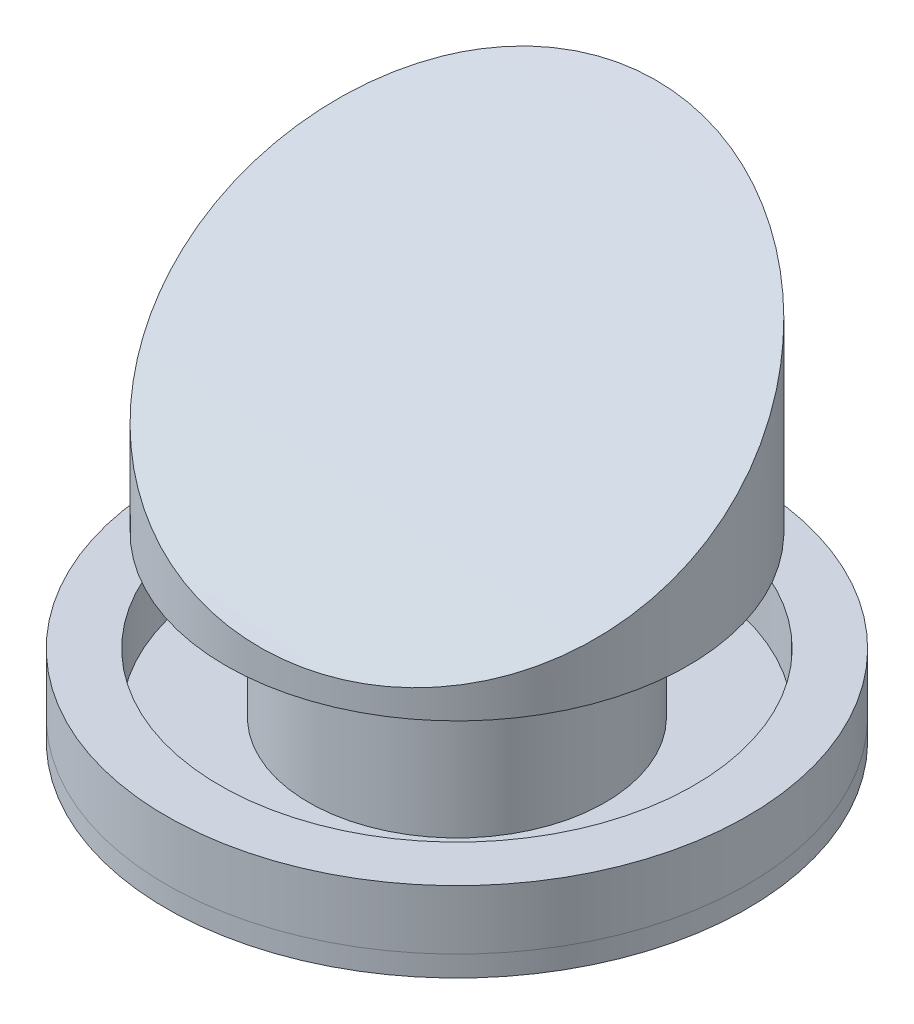
SolidWorks part; units mm, degrees
ref_plane "Plano frontal" through (0, 0, 0) normal (0, 0, 1) x (1, 0, 0)
ref_plane "Plano superior" through (0, 0, 0) normal (0, 1, 0) x (1, 0, 0)
ref_plane "Plano direito" through (0, 0, 0) normal (1, 0, 0) x (0, 0, -1)
sketch "Esboço2" plane through (0, 0, 0) normal (0, 0, 1) x (1, 0, 0)
  line L0 (0, 0) -> (0, 847.2146) construction
  line L1 (0, 0) -> (846.5488, 0) construction
  line L2 (0, 0) -> (490, 0)
  line L3 (490, 0) -> (490, 35)
  line L4 (490, 35) -> (250, 35)
  line L5 (250, 35) -> (250, 305)
  line L6 (250, 305) -> (390, 305)
  line L7 (390, 305) -> (390, 775)
  line L8 (390, 775) -> (0, 775)
  line L9 (0, 775) -> (0, 305)
  line L10 (0, 305) -> (230, 305)
  line L11 (230, 305) -> (230, 35)
  line L12 (230, 35) -> (0, 35)
  line L13 (0, 35) -> (0, 0)
  dimension "D1" = 35
  dimension "D2" = 980
  dimension "D3" = 270
  dimension "D4" = 20
  dimension "D5" = 500
  dimension "D6" = 470
  dimension "D7" = 780
revolve "Revolução1" add sketch "Esboço2" angle 360 about L0
sketch "Esboço4" plane through (0, 0, 0) normal (0, -1, 0) x (-1, 0, 0)
  circle A0 centre (0, -450) radius 12
  circle A1 centre (-139.0576, -427.9754) radius 12
  circle A2 centre (-264.5034, -364.0576) radius 12
  circle A3 centre (-364.0576, -264.5034) radius 12
  circle A4 centre (-427.9754, -139.0576) radius 12
  circle A5 centre (-450, 0) radius 12
  circle A6 centre (-427.9754, 139.0576) radius 12
  circle A7 centre (-364.0576, 264.5034) radius 12
  circle A8 centre (-264.5034, 364.0576) radius 12
  circle A9 centre (-139.0576, 427.9754) radius 12
  circle A10 centre (0, 450) radius 12
  circle A11 centre (139.0576, 427.9754) radius 12
  circle A12 centre (264.5034, 364.0576) radius 12
  circle A13 centre (364.0576, 264.5034) radius 12
  circle A14 centre (427.9754, 139.0576) radius 12
  circle A15 centre (450, 0) radius 12
  circle A16 centre (427.9754, -139.0576) radius 12
  circle A17 centre (364.0576, -264.5034) radius 12
  circle A18 centre (264.5034, -364.0576) radius 12
  circle A19 centre (139.0576, -427.9754) radius 12
  point P43 (0, 0)
  dimension "D1" = 24
  dimension "D2" = 450
  dimension "D3" = 20
extrude "Corte-extrusão1" cut sketch "Esboço4" against normal through all
sketch "Esboço3" plane through (0, 0, 0) normal (0, 0, 1) x (1, 0, 0)
  line L0 (0, 0) -> (0, 642.3329) construction
  line L1 (0, 0) -> (784.6657, 0) construction
  line L2 (490, 35) -> (490, 135)
  line L3 (490, 135) -> (400, 135)
  line L4 (400, 135) -> (400, 35)
  line L5 (490, 35) -> (-490, 35) construction
  line L6 (400, 35) -> (490, 35)
  dimension "D1" = 100
  dimension "D2" = 800
revolve "Revolução2" add sketch "Esboço3" angle 360 about L0
hole_wizard "Furo roscado de M20x1.01" positions "Esboço6" profile "Esboço5" tap size "M20x1.0" standard "DIN"
sketch "Esboço6" plane through (0, 35, 0) normal (0, -1, 0) x (-1, 0, 0)
  point P0 (0, -450)
  point P8 (-139.0576, -427.9754)
  point P9 (-264.5034, -364.0576)
  point P10 (-364.0576, -264.5034)
  point P11 (-427.9754, -139.0576)
  point P12 (-450, 0)
  point P13 (-427.9754, 139.0576)
  point P14 (-364.0576, 264.5034)
  point P15 (-264.5034, 364.0576)
  point P16 (-139.0576, 427.9754)
  point P17 (0, 450)
  point P18 (139.0576, 427.9754)
  point P19 (264.5034, 364.0576)
  point P20 (364.0576, 264.5034)
  point P21 (427.9754, 139.0576)
  point P22 (450, 0)
  point P23 (427.9754, -139.0576)
  point P24 (364.0576, -264.5034)
  point P25 (264.5034, -364.0576)
  point P26 (139.0576, -427.9754)
  point P27 (0, 0)
  dimension "D1" = 450
  dimension "D2" = 20
cosmetic thread "Rosca de furo1" parameters "D1"=40.17, "D2"=20
cosmetic thread "Rosca de furo2" parameters "D1"=40.17, "D2"=20
cosmetic thread "Rosca de furo3" parameters "D1"=40.17, "D2"=20
cosmetic thread "Rosca de furo4" parameters "D1"=40.17, "D2"=20
cosmetic thread "Rosca de furo5" parameters "D1"=40.17, "D2"=20
cosmetic thread "Rosca de furo6" parameters "D1"=40.17, "D2"=20
cosmetic thread "Rosca de furo7" parameters "D1"=40.17, "D2"=20
cosmetic thread "Rosca de furo8" parameters "D1"=40.17, "D2"=20
cosmetic thread "Rosca de furo9" parameters "D1"=40.17, "D2"=20
cosmetic thread "Rosca de furo10" parameters "D1"=40.17, "D2"=20
cosmetic thread "Rosca de furo11" parameters "D1"=40.17, "D2"=20
cosmetic thread "Rosca de furo12" parameters "D1"=40.17, "D2"=20
cosmetic thread "Rosca de furo13" parameters "D1"=40.17, "D2"=20
cosmetic thread "Rosca de furo14" parameters "D1"=40.17, "D2"=20
cosmetic thread "Rosca de furo15" parameters "D1"=40.17, "D2"=20
cosmetic thread "Rosca de furo16" parameters "D1"=40.17, "D2"=20
cosmetic thread "Rosca de furo17" parameters "D1"=40.17, "D2"=20
cosmetic thread "Rosca de furo18" parameters "D1"=40.17, "D2"=20
cosmetic thread "Rosca de furo19" parameters "D1"=40.17, "D2"=20
cosmetic thread "Rosca de furo20" parameters "D1"=40.17, "D2"=20
sketch "Esboço5" plane through (0, 35, 450) normal (1, 0, 0) x (0, 0, -1)
  line L0 (0, 0) -> (0, 50.8782)
  line L1 (0, 50.8782) -> (9.5, 45.17)
  line L2 (9.5, 45.17) -> (9.5, 0)
  line L5 (9.5, 0) -> (0, 0)
  line L10 (0, 50.8782) -> (-9.5, 45.17) construction
  line L11 (0, -6.35) -> (0, 107.95) construction
  dimension "Tap Drill Dia." = 19
  dimension "Tap Drill Depth" = 45.17
  dimension "Drill Angle" = 118
sketch3d "3DSketch1"
  line L0 (-8570, 0, 0) -> (-8570, 0, 2200) construction
  line L1 (-8570, 0, 0) -> (0, 0, 0) construction
  line L2 (-8570, 0, 2200) -> (-8570, 5159, 2200) construction
  point P0 (-8570, 5159, 2200)
  dimension "D1" = 8570
  dimension "D2" = 2200
  dimension "D3" = 5159
ref_plane "Plano1" through (0, 0, 2200) normal (0, 0, 1) x (1, 0, 0)
sketch "Esboço10" plane through (0, 0, 2200) normal (0, 0, 1) x (1, 0, 0)
  line L0 (-5755, 9250) -> (1345, 10524)
  line L4 (1345, 10524) -> (1345, 5159)
  line L5 (1345, 5159) -> (-5755, 5159)
  line L6 (-5755, 5159) -> (-5755, 9250)
  dimension "D1" = 2815
  dimension "D2" = 4091
  dimension "D3" = 7100
  dimension "D4" = 5365
revolve "Corte-Revolução1" cut sketch "Esboço10" angle 360 about L5
